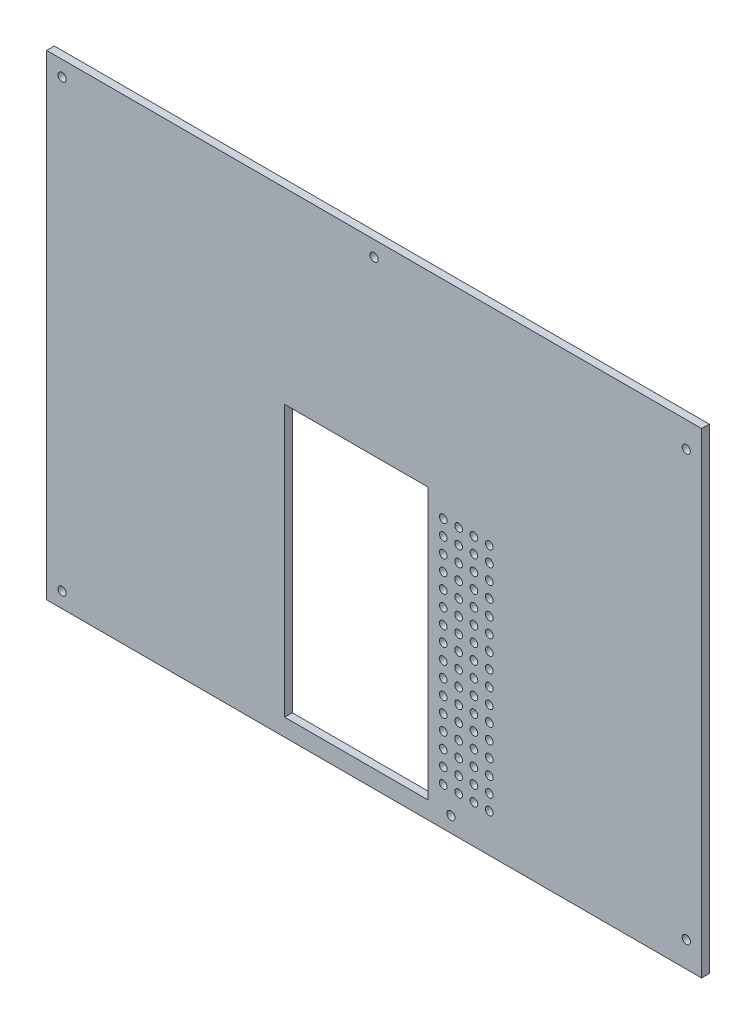
SolidWorks part; units mm, degrees
ref_plane "Front Plane" through (0, 0, 0) normal (0, 0, 1) x (1, 0, 0)
ref_plane "Top Plane" through (0, 0, 0) normal (0, 1, 0) x (1, 0, 0)
ref_plane "Right Plane" through (0, 0, 0) normal (1, 0, 0) x (0, 0, -1)
sketch "Sketch2" plane through (0, 0, 0) normal (0, 0, 1) x (1, 0, 0)
  line L1 (0, 0) -> (256, 0)
  line L2 (0, 0) -> (0, 186)
  line L3 (0, 186) -> (256, 186)
  line L4 (256, 0) -> (256, 186)
  dimension "D1" = 256
  dimension "D2" = 186
extrude "Boss-Extrude1" add sketch "Sketch2" along normal blind 3
sketch "Sketch3" plane through (0, 0, 3) normal (0, 0, 1) x (1, 0, 0)
  line L0 (6, 180) -> (128, 180) construction
  line L1 (128, 180) -> (128, 6) construction
  line L2 (128, 6) -> (6, 6) construction
  line L3 (6, 6) -> (6, 180) construction
  line L4 (250, 176) -> (250, 10) construction
  line L5 (0, 186) -> (0, 0) construction
  line L7 (0, 0) -> (256, 0) construction
  line L8 (256, 186) -> (0, 186) construction
  circle A0 centre (6, 180) radius 1.6
  circle A1 centre (128, 180) radius 1.6
  circle A3 centre (6, 6) radius 1.6
  circle A4 centre (250, 176) radius 1.6
  circle A5 centre (250, 10) radius 1.6
  circle A6 centre (158, 6) radius 1.6
  dimension "D1" = 3.2
  dimension "D6" = 10
  dimension "D8" = 10
  dimension "D10" = 3.2
  dimension "D2" = 6
  dimension "D3" = 128
  dimension "D4" = 250
  dimension "D5" = 6
  dimension "D7" = 6
  dimension "D9" = 158
extrude "Cut-Extrude1" cut sketch "Sketch3" against normal through all
sketch "Sketch4" plane through (0, 0, 3) normal (0, 0, 1) x (1, 0, 0)
  line L0 (0, 186) -> (0, 0) construction
  line L1 (93, 112.7) -> (149, 112.7)
  line L2 (93, 112.7) -> (93, 6.8)
  line L3 (93, 6.8) -> (149, 6.8)
  line L4 (149, 112.7) -> (149, 6.8)
  line L5 (0, 0) -> (256, 0) construction
  dimension "D1" = 93
  dimension "D2" = 149
  dimension "D3" = 6.8
  dimension "D4" = 112.7
extrude "Cut-Extrude2" cut sketch "Sketch4" against normal through all
sketch "Sketch5" plane through (0, 0, 3) normal (0, 0, 1) x (1, 0, 0)
  line L0 (256, 0) -> (256, 186) construction
  line L1 (0, 0) -> (256, 0) construction
  circle A0 centre (173, 105) radius 1.5
  circle A1 centre (167, 105) radius 1.5
  circle A2 centre (161, 105) radius 1.5
  circle A3 centre (155, 105) radius 1.5
  circle A4 centre (167, 99) radius 1.5
  circle A5 centre (161, 99) radius 1.5
  circle A6 centre (155, 99) radius 1.5
  circle A7 centre (167, 93) radius 1.5
  circle A8 centre (161, 93) radius 1.5
  circle A9 centre (155, 93) radius 1.5
  circle A10 centre (167, 87) radius 1.5
  circle A11 centre (161, 87) radius 1.5
  circle A12 centre (155, 87) radius 1.5
  circle A13 centre (167, 81) radius 1.5
  circle A14 centre (161, 81) radius 1.5
  circle A15 centre (155, 81) radius 1.5
  circle A16 centre (167, 75) radius 1.5
  circle A17 centre (161, 75) radius 1.5
  circle A18 centre (155, 75) radius 1.5
  circle A19 centre (167, 69) radius 1.5
  circle A20 centre (161, 69) radius 1.5
  circle A21 centre (155, 69) radius 1.5
  circle A22 centre (167, 63) radius 1.5
  circle A23 centre (161, 63) radius 1.5
  circle A24 centre (155, 63) radius 1.5
  circle A25 centre (167, 57) radius 1.5
  circle A26 centre (161, 57) radius 1.5
  circle A27 centre (155, 57) radius 1.5
  circle A28 centre (167, 51) radius 1.5
  circle A29 centre (161, 51) radius 1.5
  circle A30 centre (155, 51) radius 1.5
  circle A31 centre (167, 45) radius 1.5
  circle A32 centre (161, 45) radius 1.5
  circle A33 centre (155, 45) radius 1.5
  circle A34 centre (167, 39) radius 1.5
  circle A35 centre (161, 39) radius 1.5
  circle A36 centre (155, 39) radius 1.5
  circle A37 centre (167, 33) radius 1.5
  circle A38 centre (161, 33) radius 1.5
  circle A39 centre (155, 33) radius 1.5
  circle A40 centre (167, 27) radius 1.5
  circle A41 centre (161, 27) radius 1.5
  circle A42 centre (155, 27) radius 1.5
  circle A43 centre (167, 21) radius 1.5
  circle A44 centre (161, 21) radius 1.5
  circle A45 centre (155, 21) radius 1.5
  circle A46 centre (167, 15) radius 1.5
  circle A47 centre (161, 15) radius 1.5
  circle A48 centre (155, 15) radius 1.5
  circle A49 centre (173, 99) radius 1.5
  circle A50 centre (173, 93) radius 1.5
  circle A51 centre (173, 87) radius 1.5
  circle A52 centre (173, 81) radius 1.5
  circle A53 centre (173, 75) radius 1.5
  circle A54 centre (173, 69) radius 1.5
  circle A55 centre (173, 63) radius 1.5
  circle A56 centre (173, 57) radius 1.5
  circle A57 centre (173, 51) radius 1.5
  circle A58 centre (173, 45) radius 1.5
  circle A59 centre (173, 39) radius 1.5
  circle A60 centre (173, 33) radius 1.5
  circle A61 centre (173, 27) radius 1.5
  circle A62 centre (173, 21) radius 1.5
  circle A63 centre (173, 15) radius 1.5
  dimension "D1" = 83
  dimension "D2" = 3
  dimension "D5" = 105
  dimension "D3" = 4
  dimension "D4" = 16
extrude "Cut-Extrude3" cut sketch "Sketch5" against normal through all
